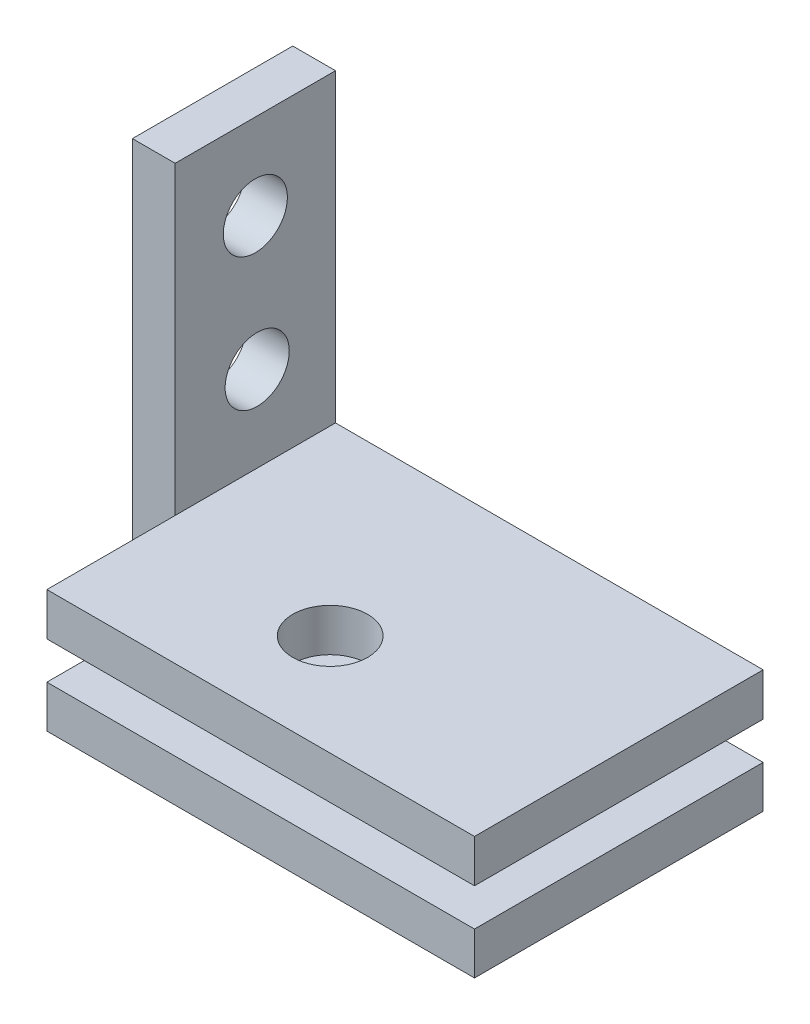
SolidWorks part; units mm, degrees
ref_plane "Front Plane" through (0, 0, 0) normal (0, 0, 1) x (1, 0, 0)
ref_plane "Top Plane" through (0, 0, 0) normal (0, 1, 0) x (1, 0, 0)
ref_plane "Right Plane" through (0, 0, 0) normal (1, 0, 0) x (0, 0, -1)
sketch "Sketch1" plane through (0, 0, 0) normal (1, 0, 0) x (0, 0, -1)
  line L1 (-0.7404, 9.0244) -> (6.7596, 9.0244)
  line L2 (-0.7404, 9.0244) -> (-0.7404, -10.9756)
  line L3 (-0.7404, -10.9756) -> (6.7596, -10.9756)
  line L4 (6.7596, 9.0244) -> (6.7596, -10.9756)
  dimension "D1" = 20
  dimension "D2" = 7.5
extrude "Boss-Extrude2" add sketch "Sketch1" along normal blind 2
sketch "Sketch2" plane through (2, 0, 0) normal (1, 0, 0) x (0, 0, -1)
  line L0 (-0.7404, 9.0244) -> (-0.7404, -10.9756) construction
  line L1 (6.7596, -10.9756) -> (-0.7404, -10.9756)
  line L2 (6.7596, -10.9756) -> (6.7596, -8.9921)
  line L3 (6.7596, -8.9921) -> (-0.7404, -8.9921)
  line L4 (-0.7404, -10.9756) -> (-0.7404, -8.9921)
extrude "Boss-Extrude3" add sketch "Sketch2" along normal blind 20
sketch "Sketch3" plane through (2, 0, 0) normal (1, 0, 0) x (0, 0, -1)
  line L0 (6.7596, -8.9921) -> (6.7596, 9.0244) construction
  line L1 (-0.7404, -8.9921) -> (6.7596, -8.9921)
  line L2 (-0.7404, -8.9921) -> (-0.7404, -7.2421)
  line L3 (-0.7404, -7.2421) -> (6.7596, -7.2421)
  line L4 (6.7596, -8.9921) -> (6.7596, -7.2421)
  line L6 (-0.7404, -7.2421) -> (6.7596, -7.2421)
  line L7 (-0.7404, -7.2421) -> (-0.7404, -5.2421)
  line L8 (-0.7404, -5.2421) -> (6.7596, -5.2421)
  line L9 (6.7596, -7.2421) -> (6.7596, -5.2421)
  line M5 (6.7596, -8.9921) -> (6.7596, 9.0244)
  line M7 (-0.7404, 9.0244) -> (-0.7404, -8.9921)
  dimension "D1" = 2
  dimension "D2" = 1.75
extrude "Boss-Extrude4" add sketch "Sketch3" along normal blind 20 contours L8 L3 M7 M5
sketch "Sketch5" plane through (2, 0, 0) normal (1, 0, 0) x (0, 0, -1)
  line L0 (6.7596, -5.2421) -> (6.7596, 9.0244) construction
  line L2 (6.7596, 9.0244) -> (-0.7404, 9.0244) construction
  line L5 (-0.7404, -5.2421) -> (6.7596, -5.2421) construction
  circle A0 centre (3.0096, 5.0244) radius 1.5
  circle A1 centre (3.0965, -1.2421) radius 1.5
  dimension "D1" = 3.75
  dimension "D2" = 4
  dimension "D3" = 4
extrude "Cut-Extrude1" cut sketch "Sketch5" against normal blind 20
sketch "Sketch8" plane through (0, 0, 0.7404) normal (0, 0, 1) x (1, 0, 0)
  line L1 (2, -5.2421) -> (22, -5.2421)
  line L2 (2, -5.2421) -> (2, -7.2421)
  line L3 (2, -7.2421) -> (22, -7.2421)
  line L4 (22, -5.2421) -> (22, -7.2421)
extrude "Boss-Extrude6" add sketch "Sketch8" along normal blind 6
sketch "Sketch9" plane through (0, 0, 0.7404) normal (0, 0, 1) x (1, 0, 0)
  line L1 (2, -8.9921) -> (22, -8.9921)
  line L2 (2, -8.9921) -> (2, -10.9756)
  line L3 (2, -10.9756) -> (22, -10.9756)
  line L4 (22, -8.9921) -> (22, -10.9756)
extrude "Boss-Extrude7" add sketch "Sketch9" along normal blind 6
sketch "Sketch10" plane through (0, -5.2421, 0) normal (0, 1, 0) x (1, 0, 0)
  line L0 (2, -0.7404) -> (2, 6.7596) construction
  line L1 (22, 6.7596) -> (2, 6.7596) construction
  circle A0 centre (10.5, -1.9904) radius 1.75
  dimension "D1" = 8.5
  dimension "D2" = 8.75
extrude "Cut-Extrude2" cut sketch "Sketch10" against normal blind 6
